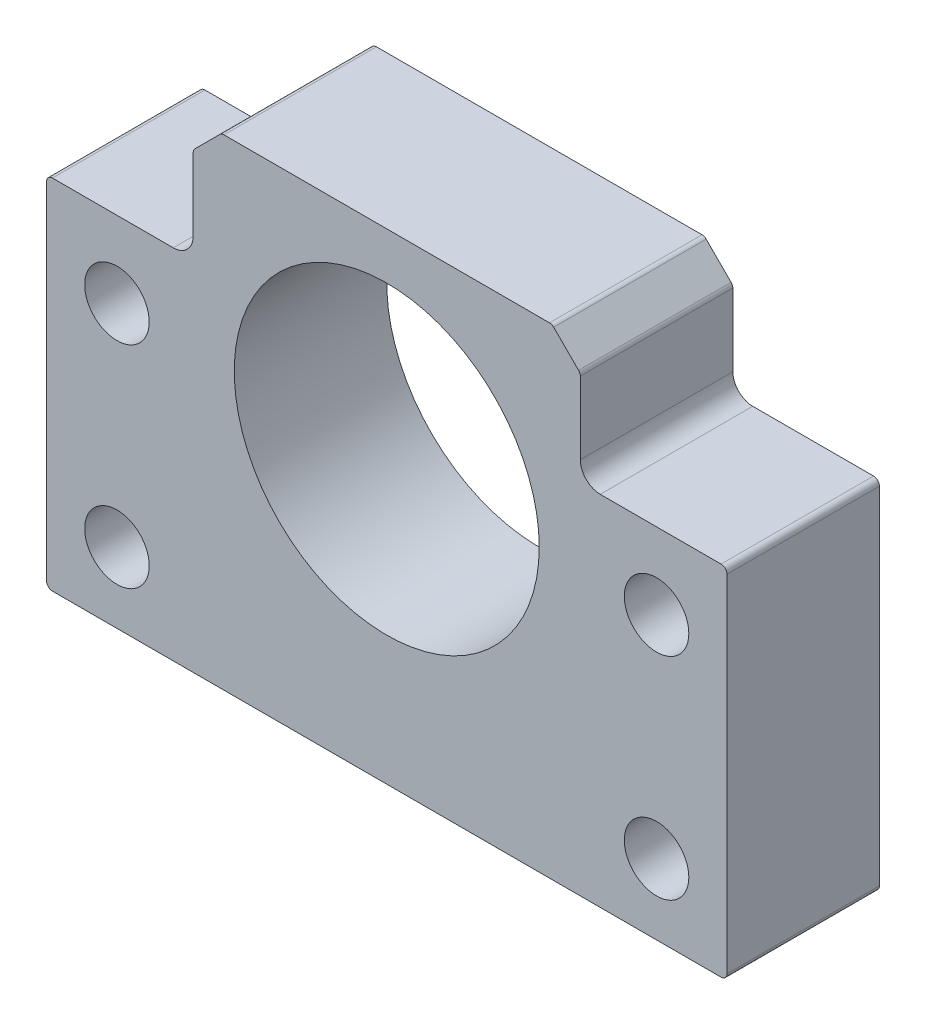
SolidWorks part; units mm, degrees
ref_plane "Front Plane" through (0, 0, 0) normal (0, 0, 1) x (1, 0, 0)
ref_plane "Top Plane" through (0, 0, 0) normal (0, 1, 0) x (1, 0, 0)
ref_plane "Right Plane" through (0, 0, 0) normal (1, 0, 0) x (0, 0, -1)
sketch "Sketch1" plane through (0, 0, 0) normal (0, 0, 1) x (1, 0, 0)
  line L20 (40.028, 14.697) -> (27.528, 14.697)
  line L21 (27.528, 14.697) -> (27.528, 22.7828)
  line L22 (27.528, 22.7828) -> (25.1138, 25.197)
  line L23 (25.1138, 25.197) -> (-3.0578, 25.197)
  line L24 (-3.0578, 25.197) -> (-5.472, 22.7828)
  line L25 (-5.472, 22.7828) -> (-5.472, 14.697)
  line L26 (-5.472, 14.697) -> (-17.972, 14.697)
  line L27 (-17.972, 14.697) -> (-17.972, -15.803)
  line L28 (-17.972, -15.803) -> (40.028, -15.803)
  line L29 (40.028, -15.803) -> (40.028, 14.697)
  circle A6 centre (34.028, 8.197) radius 2.75
  circle A7 centre (34.028, -9.803) radius 2.75
  circle A8 centre (-11.972, -9.803) radius 2.75
  circle A9 centre (-11.972, 8.197) radius 2.75
  circle A11 centre (11.028, 8.197) radius 13
  dimension "D1" = 26
  dimension "D2" = 58
  dimension "D3" = 30.5
  dimension "D4" = 30.5
  dimension "D5" = 28.1716
  dimension "D6" = 8.0858
  dimension "D7" = 12.5
  dimension "D9" = 135
  dimension "D10" = 225
  dimension "D11" = 8.0858
  dimension "D12" = 41
  dimension "D13" = 3.4142
  dimension "D14" = 3.4142
extrude "Boss-Extrude1" add sketch "Sketch1" along normal blind 13
fillet "Fillet1" radius 1.7 2 edges at (27.528, 14.697, 6.5) (-5.472, 14.697, 6.5)
fillet "Fillet2" radius 0.5 8 edges at (-17.972, 14.697, 6.5) (-17.972, -15.803, 6.5) (40.028, -15.803, 6.5) (40.028, 14.697, 6.5) (27.528, 22.7828, 6.5) (25.1138, 25.197, 6.5) (-3.0578, 25.197, 6.5) (-5.472, 22.7828, 6.5)
sketch "Sketch2" plane through (0, 0, 0) normal (0, 0, -1) x (-1, 0, 0)
  line L0 (-8.5942, -15.803) -> (17.472, -15.803)
  line L3 (-12.885, 25.197) -> (-24.9066, 25.197)
  line L4 (-40.028, -4.0931) -> (-40.028, -15.303)
  line L7 (17.972, 0.9069) -> (17.972, 14.197)
  line L8 (17.972, 14.197) -> (17.972, -15.303) construction
  line L10 (17.972, -15.303) -> (17.972, 14.197)
  line L11 (17.472, 14.697) -> (7.172, 14.697)
  line L12 (5.472, 16.397) -> (5.472, 22.5757)
  line L13 (5.3256, 22.9292) -> (3.2043, 25.0505)
  line L14 (2.8507, 25.197) -> (-24.9066, 25.197)
  line L15 (-25.2602, 25.0505) -> (-27.3815, 22.9292)
  line L16 (-27.528, 22.5757) -> (-27.528, 16.397)
  line L17 (-29.228, 14.697) -> (-39.528, 14.697)
  line L18 (-40.028, 14.197) -> (-40.028, -15.303)
  line L19 (-39.528, -15.803) -> (17.472, -15.803)
  line L20 (17.972, -15.303) -> (17.972, -4.0931)
  line L21 (17.472, 14.697) -> (7.172, 14.697)
  line L22 (5.472, 16.397) -> (5.472, 22.5757)
  line L23 (5.3256, 22.9292) -> (3.2043, 25.0505)
  line L24 (2.8507, 25.197) -> (-7.885, 25.197)
  line L25 (-25.2602, 25.0505) -> (-27.3815, 22.9292)
  line L26 (-27.528, 22.5757) -> (-27.528, 16.397)
  line L27 (-29.228, 14.697) -> (-39.528, 14.697)
  line L28 (-40.028, 14.197) -> (-40.028, 0.9069)
  line L29 (-39.528, -15.803) -> (-13.5942, -15.803)
  arc A10 (17.972, 14.197) -> (17.472, 14.697) centre (17.472, 14.197) ccw
  arc A11 (5.472, 16.397) -> (7.172, 14.697) centre (7.172, 16.397) ccw
  arc A12 (5.472, 22.5757) -> (5.3256, 22.9292) centre (4.972, 22.5757) ccw
  arc A13 (3.2043, 25.0505) -> (2.8507, 25.197) centre (2.8507, 24.697) ccw
  arc A14 (-24.9066, 25.197) -> (-25.2602, 25.0505) centre (-24.9066, 24.697) ccw
  arc A15 (-27.3815, 22.9292) -> (-27.528, 22.5757) centre (-27.028, 22.5757) ccw
  arc A16 (-29.228, 14.697) -> (-27.528, 16.397) centre (-29.228, 16.397) ccw
  arc A17 (-39.528, 14.697) -> (-40.028, 14.197) centre (-39.528, 14.197) ccw
  arc A18 (-40.028, -15.303) -> (-39.528, -15.803) centre (-39.528, -15.303) ccw
  arc A19 (17.472, -15.803) -> (17.972, -15.303) centre (17.472, -15.303) ccw
  arc A20 (17.972, 14.197) -> (17.472, 14.697) centre (17.472, 14.197) ccw
  arc A21 (5.472, 16.397) -> (7.172, 14.697) centre (7.172, 16.397) ccw
  arc A22 (5.472, 22.5757) -> (5.3256, 22.9292) centre (4.972, 22.5757) ccw
  arc A23 (3.2043, 25.0505) -> (2.8507, 25.197) centre (2.8507, 24.697) ccw
  arc A24 (-24.9066, 25.197) -> (-25.2602, 25.0505) centre (-24.9066, 24.697) ccw
  arc A25 (-27.3815, 22.9292) -> (-27.528, 22.5757) centre (-27.028, 22.5757) ccw
  arc A26 (-29.228, 14.697) -> (-27.528, 16.397) centre (-29.228, 16.397) ccw
  arc A27 (-39.528, 14.697) -> (-40.028, 14.197) centre (-39.528, 14.197) ccw
  arc A28 (-40.028, -15.303) -> (-39.528, -15.803) centre (-39.528, -15.303) ccw
  arc A29 (17.472, -15.803) -> (17.972, -15.303) centre (17.472, -15.303) ccw
  dimension "D2" = 5
  dimension "D3" = 5
  dimension "D4" = 5
  dimension "D5" = 5
  dimension "D1" = 0
sketch "Sketch3" plane through (0, 0, 0) normal (0, 0, -1) x (-1, 0, 0)
  arc A2 (-21.8167, 0.9441) -> (-0.2393, 0.9441) centre (-11.028, 8.197) ccw
  arc A4 (1.7002, 5.5526) -> (-8.5526, 20.9591) centre (-11.028, 8.197) ccw
  arc A5 (-13.5526, 20.9495) -> (-23.7562, 5.5526) centre (-11.028, 8.197) ccw
  circle A7 centre (-11.028, 8.197) radius 13 construction
  dimension "D1" = 5
  dimension "D2" = 5
  dimension "D3" = 5
